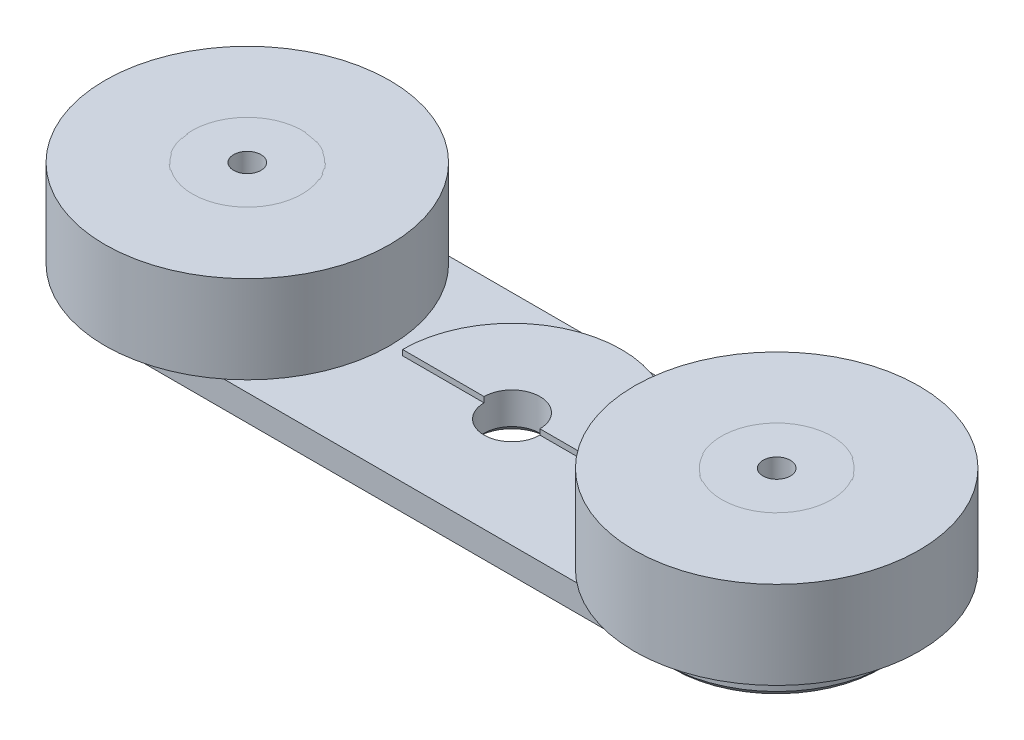
SolidWorks part; units mm, degrees
other "Rotor_1"
other "Rotor_2" parameters "D1"=10.994, "D3"=11.0231, "D4"=5, "D2"=144
ref_plane "Front Plane" through (0, 0, 0) normal (0, 0, 1) x (1, 0, 0)
ref_plane "Top Plane" through (0, 0, 0) normal (0, 1, 0) x (1, 0, 0)
ref_plane "Right Plane" through (0, 0, 0) normal (1, 0, 0) x (0, 0, -1)
sketch "Sketch1" plane through (0, 0, 0) normal (0, 1, 0) x (1, 0, 0)
  line L0 (24.175, 0) -> (-24.175, 0) construction
  line L1 (24.175, -10) -> (-24.175, -10)
  line L2 (24.175, 10) -> (-24.175, 10)
  arc A0 (24.175, -10) -> (24.175, 10) centre (24.175, 0) ccw
  arc A1 (-24.175, 10) -> (-24.175, -10) centre (-24.175, 0) ccw
  circle A2 centre (0, 0) radius 2.55
  circle A3 centre (-24.175, 0) radius 5 construction
  circle A4 centre (24.175, 0) radius 5 construction
  point P2 (0, 0)
  dimension "D1" = 10
  dimension "D3" = 5.1
  dimension "D4" = 10
  dimension "D2" = 48.35
extrude "Boss-Extrude1" add sketch "Sketch1" along normal blind 3
sketch "Sketch10" plane through (0, 3, 0) normal (0, 1, 0) x (1, 0, 0)
  circle A0 centre (-24.175, 0) radius 7.5
  circle A1 centre (24.175, 0) radius 7.5
  dimension "D1" = 15
extrude "Boss-Extrude6" add sketch "Sketch10" along normal blind 0.2
sketch "Sketch11" plane through (0, 3.2, 0) normal (0, 1, 0) x (1, 0, 0)
  circle A0 centre (-24.175, 0) radius 5.05
  circle A1 centre (24.175, 0) radius 5.05
  dimension "D1" = 10.1
extrude "Boss-Extrude8" add sketch "Sketch11" along normal blind 8
sketch "Sketch12" plane through (0, 3.2, 0) normal (0, 1, 0) x (1, 0, 0)
  circle A0 centre (-24.175, 0) radius 5
  circle A1 centre (-24.175, 0) radius 13
  dimension "D1" = 26
  dimension "D2" = 10
extrude "Boss-Extrude9" add sketch "Sketch12" along normal blind 8 separate body
mirror "Mirror3" about plane through (0, 0, 0) normal (1, 0, 0) of bodies 113
sketch "Sketch13" plane through (0, 11.2, 0) normal (0, 1, 0) x (1, 0, 0)
  circle A0 centre (-24.175, 0) radius 1.25
  circle A1 centre (24.175, 0) radius 1.25
  dimension "D1" = 2.5
extrude "Cut-Extrude6" cut sketch "Sketch13" against normal through all
ref_plane "Plane1" through (0, 11.4, 0) normal (0, 1, 0) x (1, 0, 0)
sketch "Sketch14" plane through (0, 11.4, 0) normal (0, 1, 0) x (1, 0, 0)
  line L2 (-24.175, -10) -> (24.175, -10)
  line L3 (24.175, 10) -> (-24.175, 10)
  line L4 (-24.175, -10) -> (24.175, -10)
  line L5 (24.175, 10) -> (-24.175, 10)
  circle A0 centre (0, 0) radius 2.55 construction
  circle A1 centre (0, 0) radius 2.55
  arc A2 (24.175, -10) -> (24.175, 10) centre (24.175, 0) ccw
  arc A3 (-24.175, 10) -> (-24.175, -10) centre (-24.175, 0) ccw
  arc A4 (24.175, -10) -> (24.175, 10) centre (24.175, 0) ccw
  arc A5 (-24.175, 10) -> (-24.175, -10) centre (-24.175, 0) ccw
  circle A8 centre (-24.175, 0) radius 1.75
  circle A9 centre (24.175, 0) radius 1.75
  dimension "D2" = 3.5
  dimension "D1" = 0
extrude "Boss-Extrude10" add sketch "Sketch14" along normal blind 3 separate body
sketch "Sketch15" plane through (0, 11.4, 0) normal (0, -1, 0) x (1, 0, 0)
  circle A2 centre (24.175, 0) radius 7.5 construction
  circle A3 centre (-24.175, 0) radius 7.5 construction
  circle A4 centre (-24.175, 0) radius 1.75 construction
  circle A5 centre (24.175, 0) radius 1.75 construction
  circle A6 centre (24.175, 0) radius 7.5
  circle A7 centre (-24.175, 0) radius 7.5
  circle A8 centre (-24.175, 0) radius 1.75
  circle A9 centre (24.175, 0) radius 1.75
extrude "Boss-Extrude11" add sketch "Sketch15" along normal blind 0.2
chamfer "Chamfer1" distance 2.5 angle 45 2 edges at (-24.175, 14.4, 1.75) (24.175, 14.4, 1.75)
chamfer "Chamfer2" distance 0.6 angle 45 5 edges at (0, 14.4, 10) (34.175, 14.4, 0) (-34.175, 14.4, 0) (0, 14.4, -10) (0, 14.4, 2.55)
sketch "Sketch16" plane through (0, 3, 0) normal (0, 1, 0) x (1, 0, 0)
  line L0 (-10, 0) -> (-2.55, 0)
  line L1 (2.55, 0) -> (10, 0)
  arc A0 (10, 0) -> (-10, 0) centre (0, 0) ccw
  circle A1 centre (0, 0) radius 2.55 construction
  arc A2 (2.55, 0) -> (-2.55, 0) centre (0, 0) ccw
  dimension "D1" = 20
extrude "Boss-Extrude12" add sketch "Sketch16" along normal blind 0.5
sketch "Sketch17" plane through (0, 11.4, 0) normal (0, -1, 0) x (1, 0, 0)
  line L4 (-2.55, 0) -> (-10, 0)
  line L5 (10, 0) -> (2.55, 0)
  line L6 (-2.55, 0) -> (-10, 0)
  line L7 (10, 0) -> (2.55, 0)
  arc A5 (-10, 0) -> (10, 0) centre (0, 0) ccw
  arc A6 (-2.55, 0) -> (2.55, 0) centre (0, 0) ccw
  arc A8 (-10, 0) -> (10, 0) centre (0, 0) ccw
  arc A9 (-2.55, 0) -> (2.55, 0) centre (0, 0) ccw
  dimension "D1" = 0
extrude "Boss-Extrude13" add sketch "Sketch17" along normal blind 0.5
chamfer "Chamfer3" distance 0.6 angle 45 7 edges at (24.175, 0, 1.25) (0, 0, 2.55) (-24.175, 0, 1.25) (34.175, 0, 0) (0, 0, -10) (0, 0, 10) (-34.175, 0, 0)
delete or keep bodies "Body-Delete/Keep 1" [suppressed] type delete bodies bodies 118
delete or keep bodies "Body-Delete/Keep 2" type delete bodies bodies 119
equation "\"D2@Sketch1\"=74.35-26"
